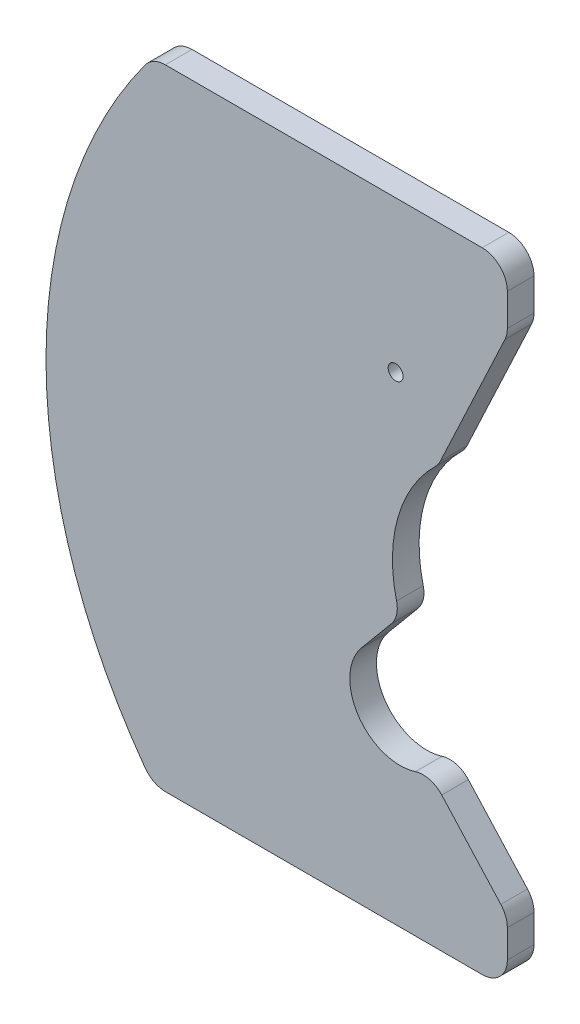
SolidWorks part; units mm, degrees
material "6061 Alloy"
ref_plane "Front Plane" through (0, 0, 0) normal (0, 0, 1) x (1, 0, 0)
ref_plane "Top Plane" through (0, 0, 0) normal (0, 1, 0) x (1, 0, 0)
ref_plane "Right Plane" through (0, 0, 0) normal (1, 0, 0) x (0, 0, -1)
other "Bounding Box"
ref_plane "Default Plane" through (-70.1042, 37.5, 0) normal (1, 0, 0) x (0, 0, -1)
sketch "Sketch1" plane through (0, 0, 0) normal (0, 0, 1) x (1, 0, 0)
  line L0 (-57.3874, 37.5) -> (-15.1374, 37.5)
  line L4 (-15.1374, -37.5) -> (-57.359, -37.5)
  line L16 (-15.1374, 37.5) -> (-15.1374, 30)
  line L19 (-15.1374, -37.5) -> (-15.1374, -30)
  line L30 (-15.1374, 30) -> (-23.3533, 12.4906)
  line L31 (-27.9226, -5.4668) -> (-32.5192, -10.9795)
  line L32 (-15.1374, -30) -> (-24.4542, -19.7261)
  arc A0 (-57.3874, 37.5) -> (-57.359, -37.5) centre (-8.5092, 0.0185) ccw
  circle A1 centre (-28.4483, 19.5) radius 0.889
  arc A6 (-23.3533, 12.4906) -> (-27.9226, -5.4668) centre (-11.8362, 0) ccw
  arc A9 (-32.5192, -10.9795) -> (-24.4542, -19.7261) centre (-27.9109, -14.8219) ccw
  dimension "D1" = 1.778
  dimension "D4" = 7.5
  dimension "D8" = 61.595
  dimension "D2" = 18
  dimension "D3" = 42.25
  dimension "D6" = 7.5
extrude "Boss-Extrude1" add sketch "Sketch1" along normal blind 3.175
fillet "Fillet1" radius 3 9 edges at (-15.1374, 37.5, 1.5875) (-57.3874, 37.5, 1.5875) (-57.359, -37.5, 1.5875) (-15.1374, -37.5, 1.5875) (-15.1374, -30, 1.5875) (-24.4542, -19.7261, 1.5875) (-27.9226, -5.4668, 1.5875) (-23.3533, 12.4906, 1.5875) (-15.1374, 30, 1.5875)
sketch "Sketch3" plane through (0, 0, 3.175) normal (0, 0, -1) x (-1, 0, 0)
  line L7 (18.1374, -37.5) -> (55.8573, -37.5)
  line L8 (18.1374, -37.5) -> (55.8573, -37.5)
  line L9 (55.8842, 37.5) -> (18.1374, 37.5)
  line L10 (55.8842, 37.5) -> (18.1374, 37.5)
  line L11 (15.4215, 29.3945) -> (23.1139, 13.0007)
  line L12 (47.4694, -37.5) -> (30.2173, -37.5)
  line L13 (45.8527, 37.5) -> (30.2173, 37.5)
  line L14 (15.4215, 29.3945) -> (23.1139, 13.0007)
  line L15 (28.9444, -6.6922) -> (32.5192, -10.9795)
  line L16 (28.9444, -6.6922) -> (32.5192, -10.9795)
  line L17 (22.9535, -21.3809) -> (15.9151, -29.1424)
  line L18 (22.9535, -21.3809) -> (15.9151, -29.1424)
  line L20 (15.1374, -31.1577) -> (15.1374, -34.5)
  line L23 (15.1374, 34.5) -> (15.1374, 30.6689)
  arc A0 (32.5973, -39.3264) -> (32.5973, 39.3264) centre (-18.6467, 0) ccw
  arc A14 (28.3352, -4.055) -> (23.7297, 12.1327) centre (11.8362, 0) ccw
  arc A15 (15.1374, -34.5) -> (18.1374, -37.5) centre (18.1374, -34.5) ccw
  arc A16 (15.1374, -34.5) -> (18.1374, -37.5) centre (18.1374, -34.5) ccw
  arc A17 (28.3352, -4.055) -> (23.7297, 12.1327) centre (11.8362, 0) ccw
  arc A18 (55.8573, -37.5) -> (58.2815, -36.2673) centre (55.8573, -34.5) ccw
  arc A19 (55.8573, -37.5) -> (58.2815, -36.2673) centre (55.8573, -34.5) ccw
  arc A20 (58.2815, -36.2673) -> (58.3098, 36.2654) centre (8.5092, 0.0185) ccw
  arc A21 (58.3098, 36.2654) -> (55.8842, 37.5) centre (55.8842, 34.5) ccw
  arc A29 (58.2815, -36.2673) -> (58.3098, 36.2654) centre (8.5092, 0.0185) ccw
  arc A31 (58.3098, 36.2654) -> (55.8842, 37.5) centre (55.8842, 34.5) ccw
  arc A32 (18.1374, 37.5) -> (15.1374, 34.5) centre (18.1374, 34.5) ccw
  arc A33 (18.1374, 37.5) -> (15.1374, 34.5) centre (18.1374, 34.5) ccw
  arc A35 (26.0875, -20.5381) -> (32.5192, -10.9795) centre (27.9109, -14.8219) ccw
  arc A36 (26.0875, -20.5381) -> (32.5192, -10.9795) centre (27.9109, -14.8219) ccw
  arc A42 (15.9151, -29.1424) -> (15.1374, -31.1577) centre (18.1374, -31.1577) ccw
  arc A43 (15.9151, -29.1424) -> (15.1374, -31.1577) centre (18.1374, -31.1577) ccw
  arc A44 (15.1374, 30.6689) -> (15.4215, 29.3945) centre (18.1374, 30.6689) ccw
  arc A45 (15.1374, 30.6689) -> (15.4215, 29.3945) centre (18.1374, 30.6689) ccw
  arc A46 (23.1139, 13.0007) -> (23.7297, 12.1327) centre (25.8298, 14.2751) ccw
  arc A47 (23.1139, 13.0007) -> (23.7297, 12.1327) centre (25.8298, 14.2751) ccw
  arc A48 (28.3352, -4.055) -> (28.9444, -6.6922) centre (31.2485, -4.771) ccw
  arc A49 (28.3352, -4.055) -> (28.9444, -6.6922) centre (31.2485, -4.771) ccw
  arc A50 (26.0875, -20.5381) -> (22.9535, -21.3809) centre (25.1758, -23.3962) ccw
  arc A51 (26.0875, -20.5381) -> (22.9535, -21.3809) centre (25.1758, -23.3962) ccw
  line M123 (18.1374, 37.5) -> (55.8842, 37.5)
  arc M124 (55.8842, 37.5) -> (58.3098, 36.2654) centre (55.8842, 34.5) cw
  arc M125 (58.3098, 36.2654) -> (58.2815, -36.2673) centre (8.5092, 0.0185) cw
  arc M126 (58.2815, -36.2673) -> (55.8573, -37.5) centre (55.8573, -34.5) cw
  line M127 (55.8573, -37.5) -> (18.1374, -37.5)
  dimension "D3" = 27.1559
  dimension "D1" = 0
extrude "Boss-Extrude3" [suppressed] add sketch "Sketch3" against normal blind 0.01 contours L8 A0 L13 M123 M124 M125 M126 M127
